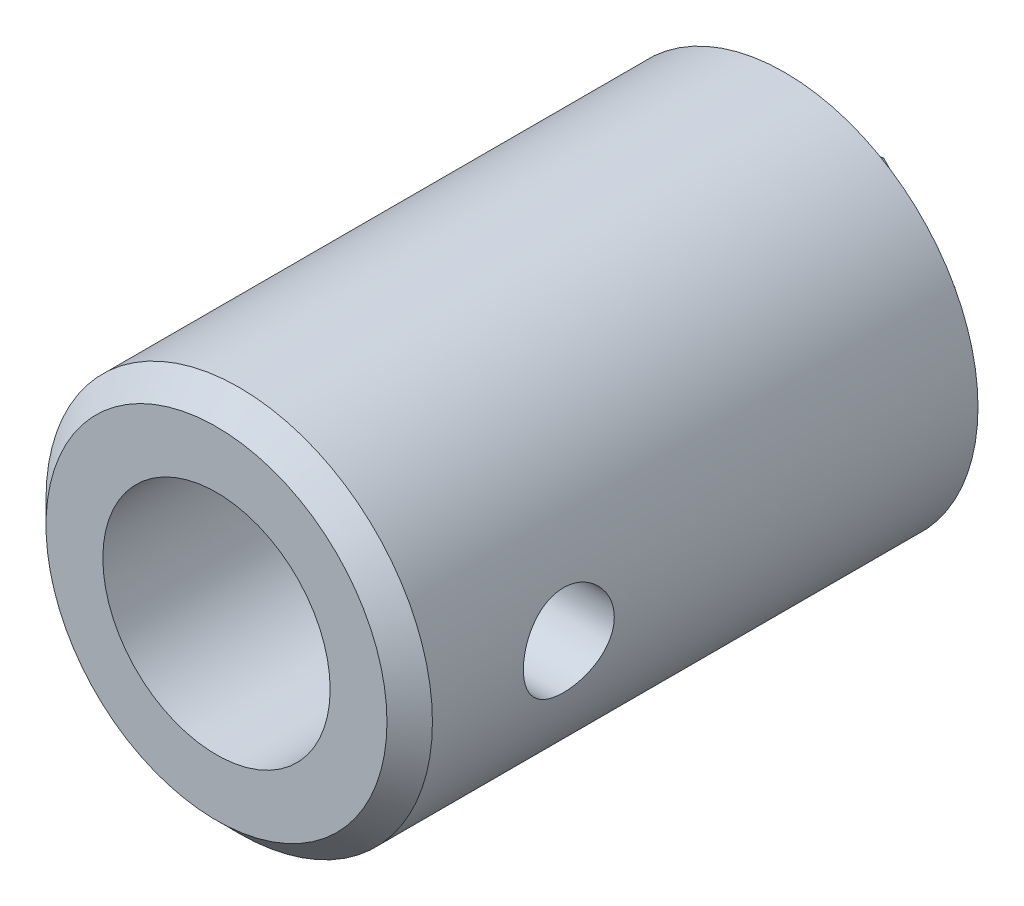
SolidWorks part; units mm, degrees
ref_plane "Front Plane" through (0, 0, 0) normal (0, 0, 1) x (1, 0, 0)
ref_plane "Top Plane" through (0, 0, 0) normal (0, 1, 0) x (1, 0, 0)
ref_plane "Right Plane" through (0, 0, 0) normal (1, 0, 0) x (0, 0, -1)
sketch "Sketch1" plane through (0, 0, 0) normal (0, 0, 1) x (1, 0, 0)
  circle A0 centre (0, 0) radius 8.5
  circle A1 centre (0, 0) radius 2
  dimension "D1" = 17
  dimension "D2" = 4
extrude "Boss-Extrude1" add sketch "Sketch1" along normal blind 5 contours A0 | A1
sketch "Sketch2" plane through (0, 0, 5) normal (0, 0, 1) x (1, 0, 0)
  circle A0 centre (0, 0) radius 8.5
  circle A1 centre (0, 0) radius 5
  dimension "D1" = 10
extrude "Boss-Extrude2" add sketch "Sketch2" along normal blind 20
sketch "Sketch3" plane through (0, 0, 0) normal (0, 0, -1) x (-1, 0, 0)
  line L1 (-4.5006, 1.0383) -> (-3.1495, -3.3785)
  line L2 (-3.1495, -3.3785) -> (1.3511, -4.4168)
  line L3 (1.3511, -4.4168) -> (4.5006, -1.0383)
  line L4 (4.5006, -1.0383) -> (3.1495, 3.3785)
  line L5 (3.1495, 3.3785) -> (-1.3511, 4.4168)
  line L6 (-1.3511, 4.4168) -> (-4.5006, 1.0383)
  circle A0 centre (0, 0) radius 4 construction
  circle A1 centre (0, 0) radius 2
  circle A2 centre (0, 0) radius 2 construction
  dimension "D1" = 8
extrude "Boss-Extrude3" add sketch "Sketch3" along normal blind 3
chamfer "Chamfer1" distance 1 angle 45 1 edges at (8.5, 0, 25)
ref_plane "Plane1" through (8.5, 0, 0) normal (1, 0, 0) x (0, 0, -1)
sketch "Sketch4" plane through (8.5, 0, 0) normal (1, 0, 0) x (0, 0, -1)
  line L0 (0, -8.5) -> (0, 8.5) construction
  circle A0 centre (-18, 0) radius 2
  dimension "D1" = 4
  dimension "D2" = 18
extrude "Cut-Extrude1" cut sketch "Sketch4" against normal up to next contours A0
